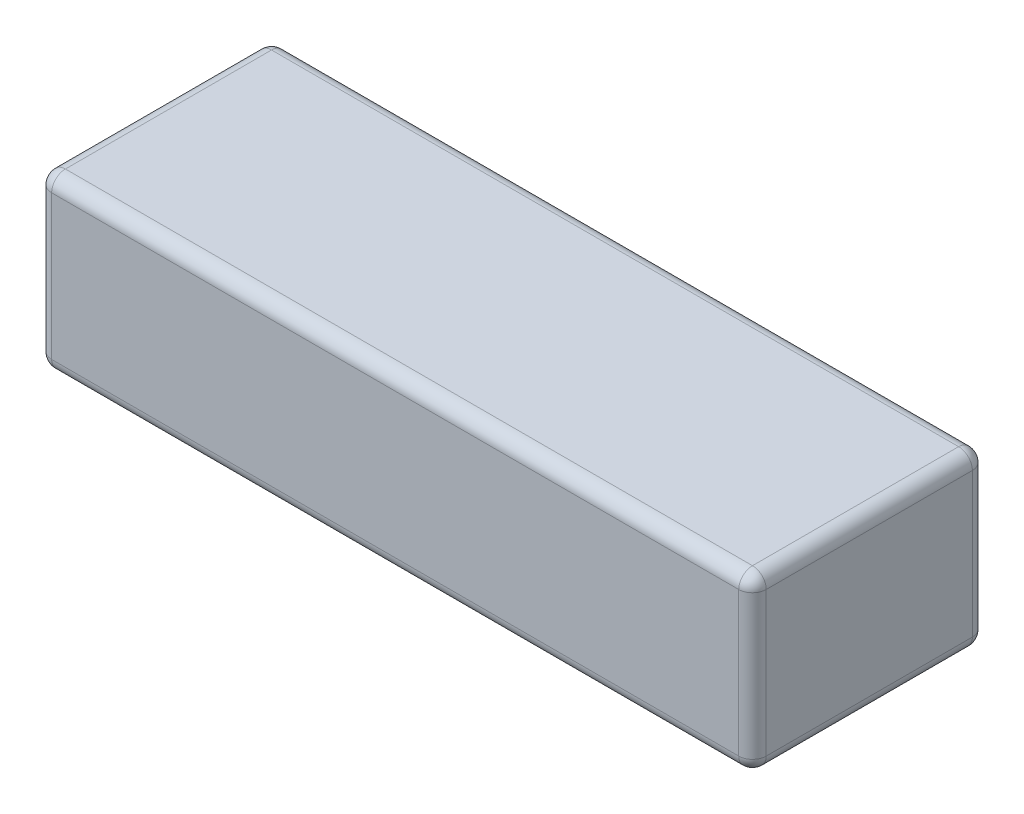
SolidWorks part; units mm, degrees
ref_plane "Front Plane" through (0, 0, 0) normal (0, 0, 1) x (1, 0, 0)
ref_plane "Top Plane" through (0, 0, 0) normal (0, 1, 0) x (1, 0, 0)
ref_plane "Right Plane" through (0, 0, 0) normal (1, 0, 0) x (0, 0, -1)
sketch "Sketch1" plane through (0, 0, 0) normal (0, 1, 0) x (1, 0, 0)
  line L1 (-52, -17) -> (52, -17)
  line L2 (-52, -17) -> (-52, 17)
  line L3 (-52, 17) -> (52, 17)
  line L4 (52, -17) -> (52, 17)
  line L5 (-52, -17) -> (52, 17) construction
  line L6 (-52, 17) -> (52, -17) construction
  point P0 (0, 0)
  dimension "D1" = 104
  dimension "D2" = 34
extrude "Boss-Extrude1" add sketch "Sketch1" along normal blind 25
fillet "Fillet1" radius 2 12 edges at (52, 12.5, -17) (-52, 12.5, -17) (-52, 12.5, 17) (52, 12.5, 17) (0, 25, 17) (-52, 25, 0) (0, 25, -17) (52, 25, 0) (0, 0, 17) (-52, 0, 0) (0, 0, -17) (52, 0, 0)
